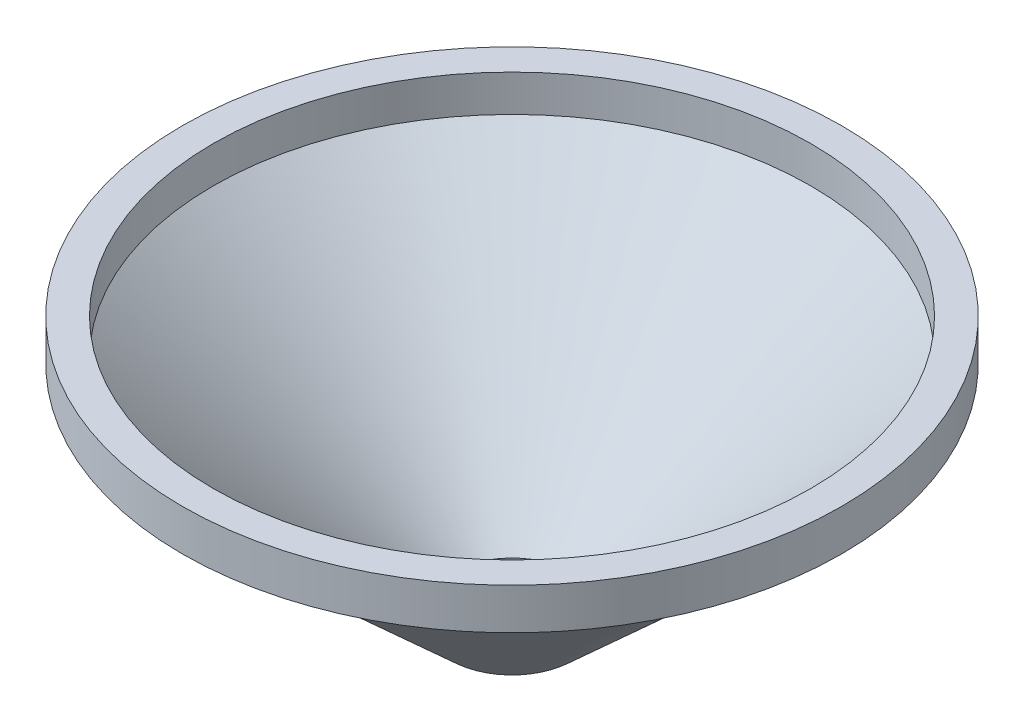
SolidWorks part; units mm, degrees
ref_plane "Front Plane" through (0, 0, 0) normal (0, 0, 1) x (1, 0, 0)
ref_plane "Top Plane" through (0, 0, 0) normal (0, 1, 0) x (1, 0, 0)
ref_plane "Right Plane" through (0, 0, 0) normal (1, 0, 0) x (0, 0, -1)
sketch "Sketch1" plane through (0, 0, 0) normal (0, 0, 1) x (1, 0, 0)
  line L0 (0, 0) -> (0, -43.5907) construction
  line L1 (15, 0) -> (15, -2)
  line L2 (15, -2) -> (1.3493, -14.4763)
  line L3 (0, 0) -> (15, 0) construction
  arc A0 (1.3493, -14.4763) -> (0, -15) centre (0, -13) cw
  dimension "D3" = 2
  dimension "D1" = 30
  dimension "D2" = 15
  dimension "D4" = 2
revolve "Revolve-Thin1" add sketch "Sketch1" angle 360 about L0
sketch "Sketch2" plane through (0, 0, 0) normal (0, 0, 1) x (1, 0, 0)
  line L0 (0, 0) -> (0, -9.4518) construction
  line L1 (-15, 0) -> (-16, 0)
  line L2 (-15, 0) -> (-15, -2)
  line L3 (-15, -2) -> (-16, -2)
  line L4 (-16, 0) -> (-16, -2)
  dimension "D1" = 32
revolve "Revolve1" add sketch "Sketch2" angle 360 about L0
sketch "Sketch3" plane through (0, 0, 0) normal (0, 1, 0) x (-1, 0, 0)
  circle A0 centre (0, 0) radius 3
  dimension "D1" = 6
extrude "Cut-Extrude1" cut sketch "Sketch3" against normal through all
